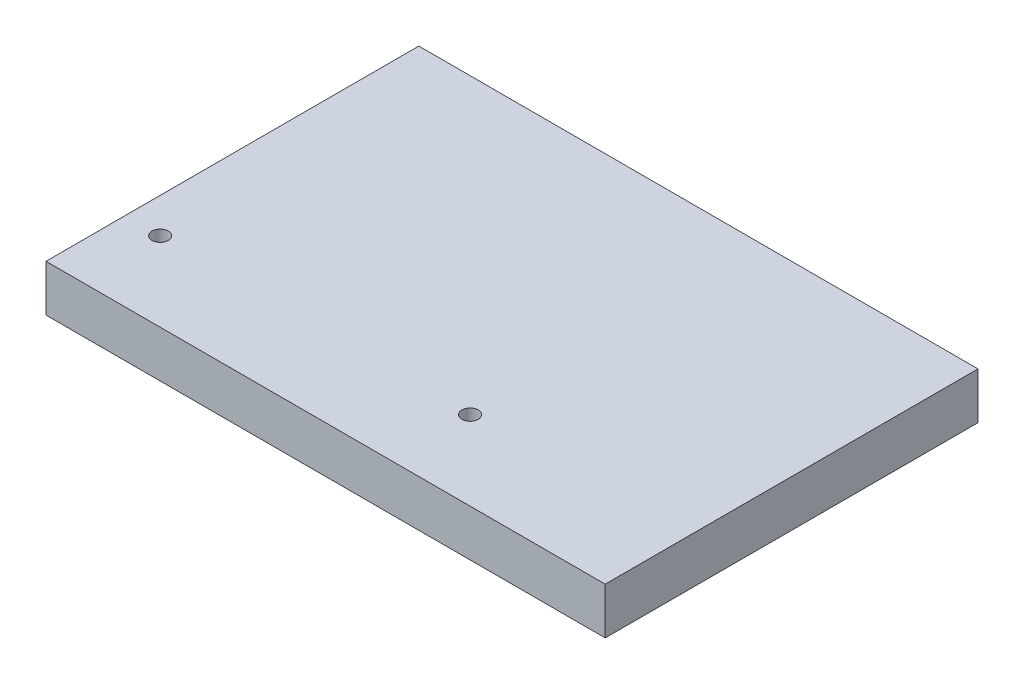
SolidWorks part; units mm, degrees
ref_plane "Front Plane" through (0, 0, 0) normal (0, 0, 1) x (1, 0, 0)
ref_plane "Top Plane" through (0, 0, 0) normal (0, 1, 0) x (1, 0, 0)
ref_plane "Right Plane" through (0, 0, 0) normal (1, 0, 0) x (0, 0, -1)
sketch "Sketch1" plane through (0, 5100, 0) normal (0, -1, 0) x (1, 0, 0)
  line L1 (-86.4895, 26.9213) -> (33.5105, 26.9213)
  line L2 (-86.4895, 26.9213) -> (-86.4895, -53.0787)
  line L3 (-86.4895, -53.0787) -> (33.5105, -53.0787)
  line L4 (33.5105, 26.9213) -> (33.5105, -53.0787)
  dimension "D1" = 80
  dimension "D2" = 120
extrude "Boss-Extrude1" add sketch "Sketch1" along normal blind 10
sketch "Sketch2" plane through (0, 5090, 0) normal (0, -1, 0) x (1, 0, 0)
  line L0 (-86.4895, 26.9213) -> (-86.4895, -53.0787) construction
  line L1 (33.5105, 26.9213) -> (-86.4895, 26.9213) construction
  circle A0 centre (-78.9895, 9.9213) radius 1.75
  circle A1 centre (-12.4895, 9.9213) radius 1.75
  dimension "D1" = 3.5
  dimension "D5" = 3.5
  dimension "D2" = 7.5
  dimension "D3" = 17
  dimension "D4" = 17
  dimension "D6" = 66.5
extrude "Cut-Extrude1" cut sketch "Sketch2" against normal through all
sketch "Sketch3" plane through (0, 5090, 0) normal (0, -1, 0) x (1, 0, 0)
  circle A0 centre (-78.9895, 9.9213) radius 3.25
  circle A1 centre (-12.4895, 9.9213) radius 3.25
  dimension "D1" = 6.5
  dimension "D2" = 6.5
extrude "Cut-Extrude2" cut sketch "Sketch3" against normal blind 5
